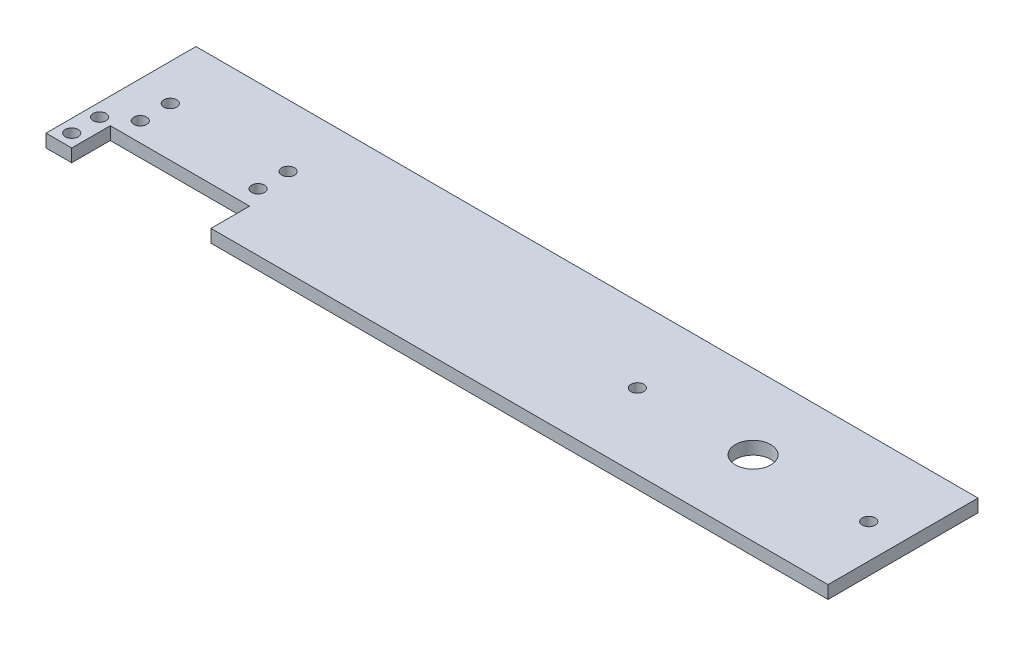
SolidWorks part; units mm, degrees
ref_plane "Front Plane" through (0, 0, 0) normal (0, 0, 1) x (1, 0, 0)
ref_plane "Top Plane" through (0, 0, 0) normal (0, 1, 0) x (1, 0, 0)
ref_plane "Right Plane" through (0, 0, 0) normal (1, 0, 0) x (0, 0, -1)
sketch "Sketch1" plane through (0, 0, 0) normal (0, 1, 0) x (1, 0, 0)
  line L0 (47.5, 13.6856) -> (47.5, -3.2344) construction
  line L1 (-100, 22.5) -> (82.5, 22.5)
  line L2 (-100, 22.5) -> (-100, -12.5)
  line L3 (-100, -12.5) -> (82.5, -12.5)
  line L4 (82.5, 22.5) -> (82.5, -12.5)
  line L6 (12.5, -1) -> (82.5, -1)
  line L7 (12.5, -1) -> (12.5, 11)
  line L8 (12.5, 11) -> (82.5, 11)
  line L9 (82.5, -1) -> (82.5, 11)
  line L10 (12.5, -1) -> (82.5, 11) construction
  line L11 (12.5, 11) -> (82.5, -1) construction
  circle A4 centre (47.5, 5) radius 4.125
  circle A5 centre (74.5, 5) radius 1.5
  circle A6 centre (20.5, 5) radius 1.5
  circle A7 centre (-97, -9.5) radius 1.5
  circle A8 centre (-97, -3) radius 1.5
  circle A9 centre (-91.5, 8) radius 1.5
  circle A10 centre (-64, 8) radius 1.5
  circle A11 centre (-64, 1) radius 1.5
  circle A12 centre (-91.5, 1) radius 1.5
  point P0 (0, 0)
  point P25 (0, 0)
  point P26 (0, 0)
  dimension "D3" = 3
  dimension "D4" = 8.25
  dimension "D5" = 3
  dimension "D9" = 3
  dimension "D13" = 3
  dimension "D1" = 35
  dimension "D2" = 182.5
  dimension "D6" = 8
  dimension "D7" = 70
  dimension "D8" = 12
  dimension "D10" = 3
  dimension "D11" = 6.5
  dimension "D12" = 3
  dimension "D14" = 14.5
  dimension "D15" = 8.5
  dimension "D18" = 27.5
  dimension "D16" = 2
  dimension "D17" = 2
extrude "Boss-Extrude1" add sketch "Sketch1" along normal blind 3 contours L7 L8 L4 L1 L2 L3 L6 | L8 L7 L6 L4 A4 A5 A6
sketch "Sketch2" plane through (0, 0, 0) normal (0, 0, 1) x (1, 0, 0)
  line L0 (-94.5, 33) -> (-94.5, -17) construction
  line L1 (-92, 33) -> (-92, -17)
  line L2 (-97, 33) -> (-97, -17)
  line L3 (-89, 33) -> (-89, -17)
  line L4 (-100, 33) -> (-100, -17)
  line L5 (-100, 3) -> (-100, 0) construction
  line L7 (-94, 6.4998) -> (-61.5, 6.4998)
  line L8 (-94, 6.4998) -> (-94, -3.3981)
  line L9 (-94, -3.3981) -> (-61.5, -3.3981)
  line L10 (-61.5, 6.4998) -> (-61.5, -3.3981)
  arc A0 (-92, 33) -> (-97, 33) centre (-94.5, 33) ccw
  arc A1 (-97, -17) -> (-92, -17) centre (-94.5, -17) ccw
  arc A2 (-100, -17) -> (-89, -17) centre (-94.5, -17) ccw
  arc A3 (-89, 33) -> (-100, 33) centre (-94.5, 33) ccw
  point P2 (-94.5, 8)
  dimension "D4" = 5.5
  dimension "D1" = 3
  dimension "D2" = 3
  dimension "D3" = 5
  dimension "D5" = 50
  dimension "D6" = 50
  dimension "D7" = 6
  dimension "D8" = 32.5
extrude "Cut-Extrude3" cut sketch "Sketch2" along normal up to surface (9 mm away) from offset 3.5 contours L1 L9 L3 L7 | L10 L7 L3 L9 | L8 L9 L1 L7 up to face at (-8.75, 1.5, 12.5)
